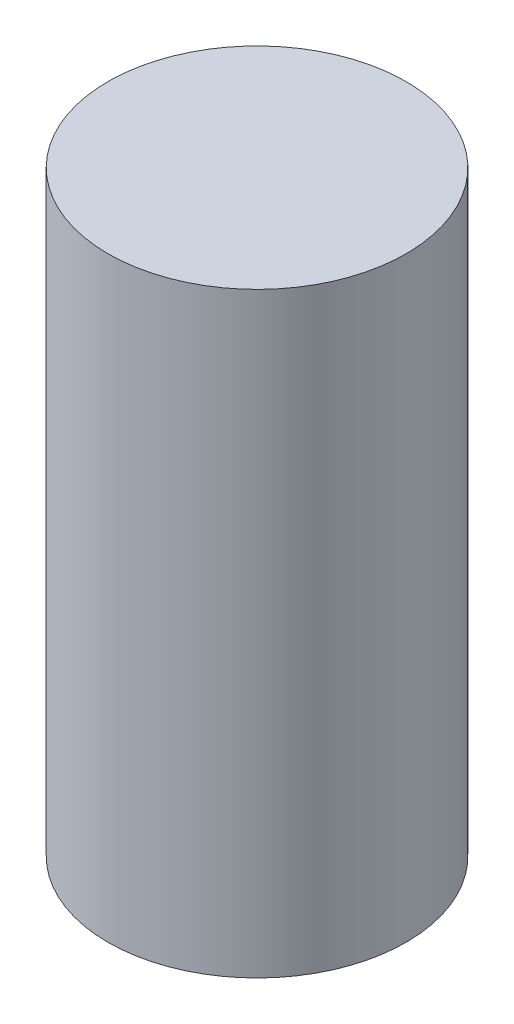
SolidWorks part; units mm, degrees
ref_plane "Alzado" through (0, 0, 0) normal (0, 0, 1) x (1, 0, 0)
ref_plane "Planta" through (0, 0, 0) normal (0, 1, 0) x (1, 0, 0)
ref_plane "Vista lateral" through (0, 0, 0) normal (1, 0, 0) x (0, 0, -1)
sketch "Croquis1" plane through (0, 0, 0) normal (0, 1, 0) x (1, 0, 0)
  circle A0 centre (0, 0) radius 2
extrude "Saliente-Extruir1" add sketch "Croquis1" along normal blind 8
